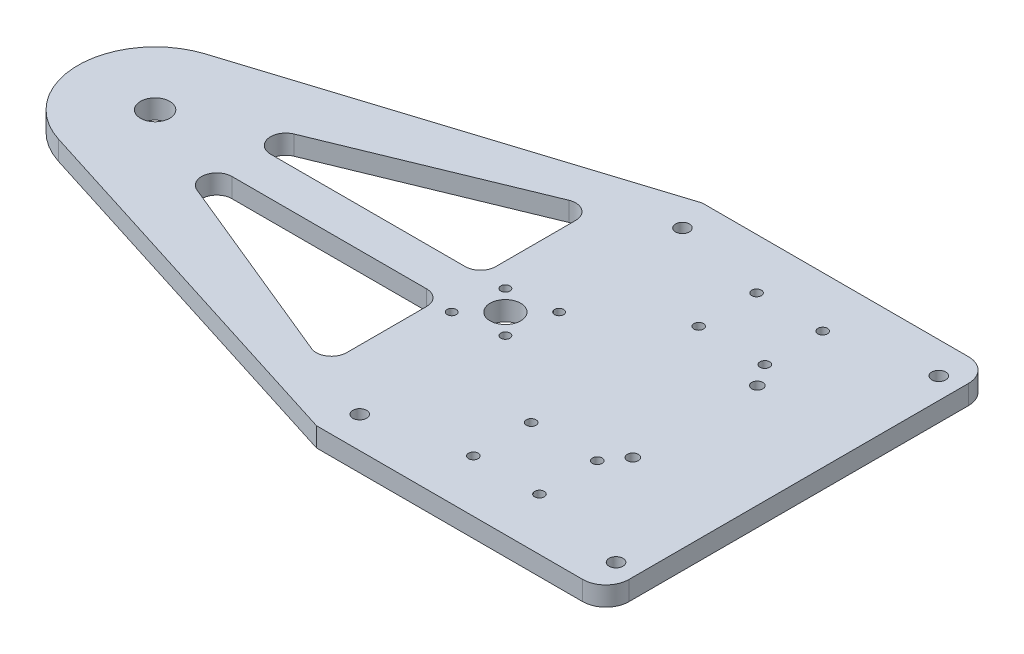
SolidWorks part; units mm, degrees
material "UHMW"
ref_plane "Front Plane" through (0, 0, 0) normal (0, 0, 1) x (1, 0, 0)
ref_plane "Top Plane" through (0, 0, 0) normal (0, 1, 0) x (1, 0, 0)
ref_plane "Right Plane" through (0, 0, 0) normal (1, 0, 0) x (0, 0, -1)
sketch "Sketch1" plane through (0, 0, 0) normal (0, 1, 0) x (1, 0, 0)
  line L0 (-47.625, 0) -> (47.625, 0) construction
  line L1 (-47.625, -63.5) -> (47.625, -63.5)
  line L2 (-47.625, -63.5) -> (-47.625, 63.5)
  line L3 (-47.625, 63.5) -> (47.625, 63.5)
  line L4 (47.625, -63.5) -> (47.625, 63.5)
  line L5 (-47.625, -63.5) -> (47.625, 63.5) construction
  line L6 (-47.625, 63.5) -> (47.625, -63.5) construction
  point P0 (0, 0)
  dimension "D1" = 95.25
  dimension "D2" = 127
  dimension "D3" = 63.5
extrude "Boss-Extrude1" add sketch "Sketch1" along normal blind 6.35
sketch "Sketch4" plane through (0, 6.35, 0) normal (0, 1, 0) x (1, 0, 0)
  line L1 (-47.625, 63.5) -> (-171.916, 24.2193)
  line L5 (-47.625, 63.5) -> (-47.625, -63.5) construction
  line L9 (-47.625, -63.5) -> (-171.916, -24.2193)
  line L10 (-47.625, 63.5) -> (-47.625, -63.5)
  arc A0 (-171.916, 24.2193) -> (-171.916, -24.2193) centre (-164.2618, 0) ccw
  circle A1 centre (-48.9458, 0) radius 2.5 construction
  dimension "D1" = 50.8
  dimension "D2" = 115.316
extrude "Boss-Extrude3" add sketch "Sketch4" against normal blind 6.35
sketch "Sketch5" plane through (0, 6.35, 0) normal (0, 1, 0) x (1, 0, 0)
  line L0 (-48.9458, 0) -> (-31.7264, 0) construction
  line L3 (-48.9458, 0) -> (-91.3931, 0) construction
  circle A0 centre (-164.2618, 0) radius 4.826
  circle A1 centre (-48.9458, 0) radius 5.04
  arc A2 (-171.916, 24.2193) -> (-171.916, -24.2193) centre (-164.2618, 0) ccw construction
  arc A3 (-171.916, 24.2193) -> (-171.916, -24.2193) centre (-164.2618, 0) ccw
  circle A4 centre (-42.2283, -6.7175) radius 1.5
  circle A5 centre (-40.107, 8.8388) radius 1.5
  circle A6 centre (-57.7846, -8.8388) radius 1.5
  circle A7 centre (-55.6633, 6.7175) radius 1.5
  circle A8 centre (-40.107, 8.8388) radius 1.5 construction
  circle A9 centre (-55.6633, 6.7175) radius 1.5 construction
  circle A10 centre (-57.7846, -8.8388) radius 1.5 construction
  circle A11 centre (-42.2283, -6.7175) radius 1.5 construction
  point P20 (-48.9458, 0)
  dimension "D1" = 9.652
  dimension "D2" = 17.2194
  dimension "D4" = 48.9458
  dimension "D3" = 10.08
extrude "Cut-Extrude1" cut sketch "Sketch5" against normal through all contours A0 | A1 | A5 | A6 | A7 | A4
sketch "Sketch6" plane through (0, 6.35, 0) normal (0, 1, 0) x (1, 0, 0)
  line L0 (-63.5, 6.35) -> (-63.5, -6.35) construction
  line L1 (-63.5, 45.1637) -> (-157.9118, 6.35)
  line L2 (-157.9118, 6.35) -> (-63.5, 6.35)
  line L3 (-63.5, 6.35) -> (-63.5, 45.1637)
  line L4 (-63.5, -6.35) -> (-63.5, -45.1637)
  line L5 (-63.5, -45.1637) -> (-157.9118, -6.35)
  line L6 (-157.9118, -6.35) -> (-63.5, -6.35)
  line L7 (0, 0) -> (-63.5, 0) construction
  line L8 (-189.6618, 75.5498) -> (-189.6618, -75.5498) construction
  line L9 (-47.625, 63.5) -> (-171.916, 24.2193) construction
  arc A0 (-171.916, 24.2193) -> (-171.916, -24.2193) centre (-164.2618, 0) ccw construction
  point P12 (-189.6618, 0)
  dimension "D1" = 31.75
  dimension "D2" = 12.7
  dimension "D3" = 12.7
  dimension "D4" = 63.5
extrude "Cut-Extrude2" cut sketch "Sketch6" against normal through all
fillet "Fillet9" radius 5 6 edges at (-157.9118, 3.175, 6.35) (-63.5, 3.175, 6.35) (-63.5, 3.175, 45.1637) (-63.5, 3.175, -6.35) (-157.9118, 3.175, -6.35) (-63.5, 3.175, -45.1637)
fillet "Fillet10" radius 7.62 2 edges at (47.625, 3.175, -63.5) (47.625, 3.175, 63.5)
sketch "Sketch7" plane through (0, 6.35, 0) normal (0, 1, 0) x (1, 0, 0)
  circle A0 centre (-43.7773, -53.1254) radius 2.2812
  circle A1 centre (-43.7773, 53.1254) radius 2.2812
  circle A2 centre (40.6023, 53.1254) radius 2.2812
  circle A3 centre (40.6023, -53.1254) radius 2.2812
  circle A4 centre (-43.7773, 53.1254) radius 2.2812 construction
  circle A5 centre (40.6023, 53.1254) radius 2.2812 construction
  circle A6 centre (40.6023, -53.1254) radius 2.2812 construction
  circle A7 centre (-43.7773, -53.1254) radius 2.2812 construction
extrude "Cut-Extrude3" cut sketch "Sketch7" against normal through all
sketch "Sketch8" plane through (0, 6.35, 0) normal (0, 1, 0) x (1, 0, 0)
  circle A0 centre (-13.2098, -27.25) radius 1.5875
  circle A1 centre (8.5646, -27.25) radius 1.5875
  circle A2 centre (8.5646, -46.3) radius 1.5875
  circle A3 centre (-13.2098, -46.3) radius 1.5875
  circle A4 centre (8.7179, 46.8) radius 1.5875
  circle A5 centre (-13.0566, 27.75) radius 1.5875
  circle A6 centre (-13.0566, 46.8) radius 1.5875
  circle A7 centre (8.7179, 27.75) radius 1.5875
  dimension "D1" = 3.175
extrude "Cut-Extrude4" cut sketch "Sketch8" against normal through all
sketch "Sketch9" plane through (0, 6.35, 0) normal (0, 1, 0) x (1, 0, 0)
  circle A0 centre (13.4994, -20.4978) radius 1.83
  circle A1 centre (13.4995, 20.5026) radius 1.83
extrude "Cut-Extrude5" cut sketch "Sketch9" against normal through all
